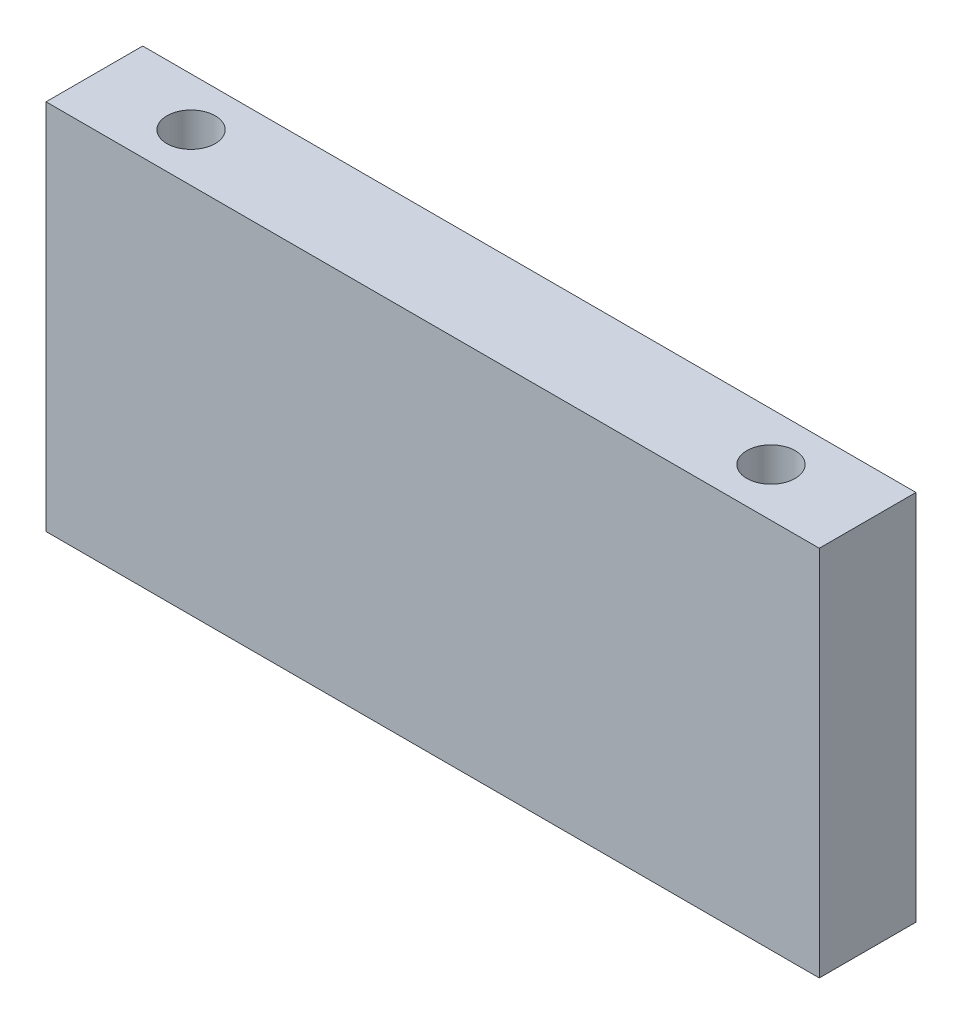
SolidWorks part; units mm, degrees
material "1060 Alloy"
ref_plane "Front Plane" through (0, 0, 0) normal (0, 0, 1) x (1, 0, 0)
ref_plane "Top Plane" through (0, 0, 0) normal (0, 1, 0) x (1, 0, 0)
ref_plane "Right Plane" through (0, 0, 0) normal (1, 0, 0) x (0, 0, -1)
sketch "Sketch1" plane through (0, 0, 0) normal (0, 1, 0) x (1, 0, 0)
  line L1 (76.2, 9.525) -> (-76.2, 9.525)
  line L2 (76.2, 9.525) -> (76.2, -9.525)
  line L3 (76.2, -9.525) -> (-76.2, -9.525)
  line L4 (-76.2, 9.525) -> (-76.2, -9.525)
  line L5 (76.2, 9.525) -> (-76.2, -9.525) construction
  line L6 (76.2, -9.525) -> (-76.2, 9.525) construction
  point P0 (0, 0)
  dimension "D1" = 19.05
  dimension "D2" = 152.4
extrude "Boss-Extrude1" add sketch "Sketch1" along normal mid plane 73.3552
sketch "Sketch2" plane through (0, 36.6776, 0) normal (0, 1, 0) x (1, 0, 0)
  line L0 (-57.15, 0) -> (57.15, 0) construction
  line L1 (0, -55) -> (0, 55) construction
  line L2 (-55, 0) -> (55, 0) construction
  circle A0 centre (-57.15, 0) radius 4.7625
  circle A1 centre (57.15, 0) radius 4.7625
  point P4 (0, 0)
  dimension "D2" = 9.525
  dimension "D1" = 114.3
extrude "Cut-Extrude1" cut sketch "Sketch2" against normal blind 19.05
mirror "Mirror2" about plane through (0, 0, 0) normal (0, 1, 0) of "Cut-Extrude1"
